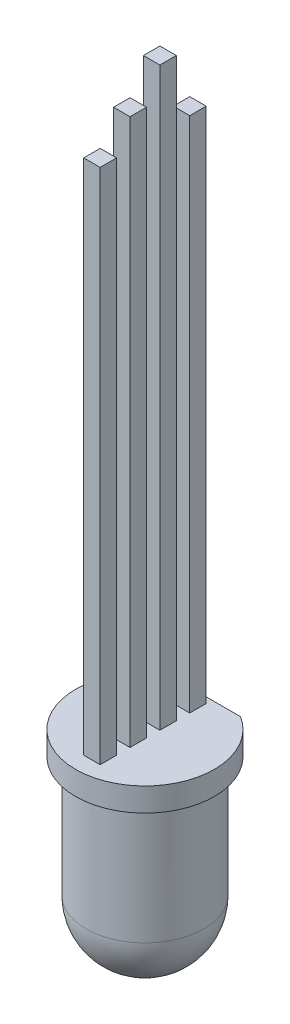
SolidWorks part; units mm, degrees
ref_plane "Plan de face" through (0, 0, 0) normal (0, 0, 1) x (1, 0, 0)
ref_plane "Plan de dessus" through (0, 0, 0) normal (0, 1, 0) x (1, 0, 0)
ref_plane "Plan de droite" through (0, 0, 0) normal (1, 0, 0) x (0, 0, -1)
sketch "Esquisse1" plane through (0, 0, 0) normal (0, 0, 1) x (1, 0, 0)
  line L0 (2.5, 7.6) -> (2.5, 2.5)
  line L1 (2.5, 7.6) -> (2.95, 7.6)
  line L2 (2.95, 7.6) -> (2.95, 8.6)
  line L3 (2.95, 8.6) -> (0, 8.6)
  line L4 (0, 0) -> (0, 10.615) construction
  line L5 (0, 0) -> (0, 8.6)
  arc A0 (2.5, 2.5) -> (0, 0) centre (0, 2.5) cw
  dimension "D1" = 2.5
  dimension "D2" = 7.6
  dimension "D3" = 90
  dimension "D4" = 0.45
  dimension "D5" = 1
  dimension "D6" = 5.9
revolve "Révolution1" add sketch "Esquisse1" angle 360 about L4
sketch "Esquisse2" plane through (0, 7.6, 0) normal (0, -1, 0) x (-1, 0, 0)
  line L0 (2.0316, 2.5) -> (-2.1192, 2.5)
  line L1 (2.0316, 2.5) -> (-0.3043, 5.4158)
  line L2 (-0.3043, 5.4158) -> (-2.1192, 2.5)
  circle A0 centre (0, 0) radius 2.5 construction
extrude "Enlèv. mat.-Extru.1" cut sketch "Esquisse2" against normal up to next
sketch "Esquisse3" plane through (0, 8.6, 0) normal (0, 1, 0) x (1, 0, 0)
  line L0 (-0.35, 2.255) -> (0.35, 2.255)
  line L1 (0.35, 2.255) -> (0.35, 1.555)
  line L2 (0.35, 1.555) -> (-0.35, 1.555)
  line L3 (-0.35, 1.555) -> (-0.35, 2.255)
  line L4 (-0.35, -0.985) -> (0.35, -0.985)
  line L5 (0.35, -0.985) -> (0.35, -0.285)
  line L6 (0.35, -0.285) -> (-0.35, -0.285)
  line L7 (-0.35, -0.285) -> (-0.35, -0.985)
  line L8 (-0.35, -1.555) -> (0.35, -1.555)
  line L9 (0.35, -1.555) -> (0.35, -2.255)
  line L10 (0.35, -2.255) -> (-0.35, -2.255)
  line L11 (-0.35, -2.255) -> (-0.35, -1.555)
  line L12 (-0.35, 0.985) -> (0.35, 0.985)
  line L13 (0.35, 0.985) -> (0.35, 0.285)
  line L14 (0.35, 0.285) -> (-0.35, 0.285)
  line L15 (-0.35, 0.285) -> (-0.35, 0.985)
  line L16 (0, 2.8041) -> (0, -3.2431) construction
  dimension "D1" = 0.7
  dimension "D2" = 0.7
  dimension "D3" = 0.35
  dimension "D4" = 0.35
  dimension "D5" = 0.35
  dimension "D6" = 0.7
  dimension "D7" = 0.7
  dimension "D8" = 0.7
  dimension "D9" = 0.7
  dimension "D10" = 0.35
  dimension "D11" = 1.27
  dimension "D12" = 0.7
  dimension "D13" = 0.7
  dimension "D14" = 1.27
  dimension "D15" = 1.27
  dimension "D16" = 0.285
extrude "Boss.-Extru.1" add sketch "Esquisse3" along normal blind 24.5
sketch "Esquisse4" plane through (-0.35, 0, 0) normal (-1, 0, 0) x (0, 0, 1)
  line L0 (-2.8851, 30.6) -> (-1.2657, 30.6)
  line L1 (-1.2657, 30.6) -> (-1.2657, 33.9219)
  line L2 (-1.2657, 33.9219) -> (0, 33.9219)
  line L3 (0, 33.9219) -> (0, 31.83)
  line L4 (0, 31.83) -> (1.3444, 31.83)
  line L5 (1.3444, 31.83) -> (1.3444, 30.6)
  line L6 (1.3444, 30.6) -> (2.8975, 30.6)
  line L7 (2.8975, 30.6) -> (2.8975, 34.6769)
  line L8 (2.8975, 34.6769) -> (-2.8851, 34.6769)
  line L9 (-2.8851, 34.6769) -> (-2.8851, 30.6)
  line L10 (-0.985, 33.1) -> (-0.285, 33.1) construction
  line L11 (0.285, 33.1) -> (0.985, 33.1) construction
  dimension "D1" = 2.5
  dimension "D2" = 2.5
  dimension "D3" = 1.27
extrude "Enlèv. mat.-Extru.2" cut sketch "Esquisse4" against normal up to next
